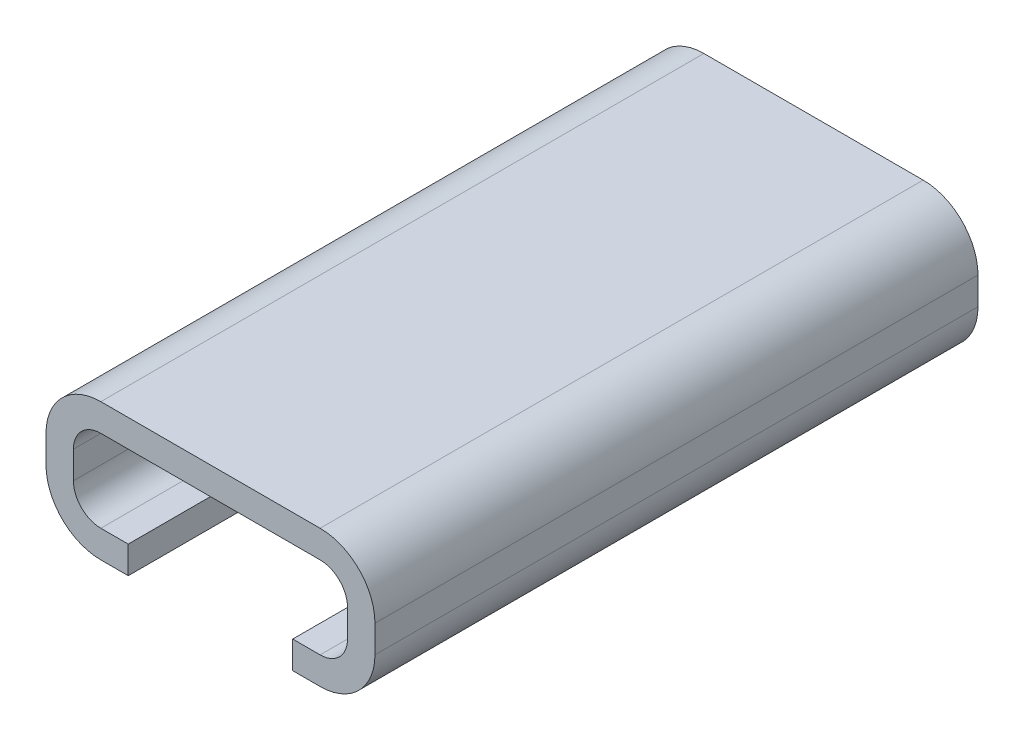
SolidWorks part; units mm, degrees
ref_plane "Plan de face" through (0, 0, 0) normal (0, 0, 1) x (1, 0, 0)
ref_plane "Plan de dessus" through (0, 0, 0) normal (0, 1, 0) x (1, 0, 0)
ref_plane "Plan de droite" through (0, 0, 0) normal (1, 0, 0) x (0, 0, -1)
sketch "Esquisse1" plane through (0, 0, 0) normal (0, 0, 1) x (1, 0, 0)
  line L1 (5, 0.5) -> (5, -0.5)
  line L2 (4, -1.5) -> (-4, -1.5)
  line L3 (-5, -0.5) -> (-5, 0.5)
  line L5 (6, 0.5) -> (6, -0.5)
  line L6 (4, -2.5) -> (-4, -2.5)
  line L7 (-6, -0.5) -> (-6, 0.5)
  line L16 (-4, 2.5) -> (4, 2.5) construction
  line L17 (4, 2.5) -> (-2.2321, 2.5)
  line L18 (-4, 2.5) -> (-2.2321, 2.5)
  line L19 (-4, 1.5) -> (4, 1.5)
  line L20 (-4, 1.5) -> (4, 1.5) construction
  arc A0 (-4, -1.5) -> (-5, -0.5) centre (-4, -0.5) cw
  arc A1 (5, -0.5) -> (4, -1.5) centre (4, -0.5) cw
  arc A2 (4, 1.5) -> (5, 0.5) centre (4, 0.5) cw
  arc A3 (-4, 1.5) -> (-5, 0.5) centre (-4, 0.5) ccw
  arc A4 (4, 2.5) -> (6, 0.5) centre (4, 0.5) cw
  arc A5 (6, -0.5) -> (4, -2.5) centre (4, -0.5) cw
  arc A6 (-4, -2.5) -> (-6, -0.5) centre (-4, -0.5) cw
  arc A7 (-4, 2.5) -> (-6, 0.5) centre (-4, 0.5) ccw
  point P6 (-5, -1.5)
  point P11 (5.1, 1.6)
  point P14 (-5, 1.5)
  point P15 (0, 1.5)
  point P16 (-5, 0)
  dimension "D3" = 1
  dimension "D1" = 3
  dimension "D2" = 10
  dimension "D9" = 3
  dimension "D4" = 1
extrude "Boss.-Extru.2" add sketch "Esquisse1" along normal blind 10
sketch "Esquisse7" plane through (0, 0, 0) normal (0, 0, -1) x (-1, 0, 0)
  line L8 (-6, 0.5) -> (-6, -0.5)
  line L9 (-4, -2.5) -> (4, -2.5)
  line L10 (6, -0.5) -> (6, 0.5)
  line L11 (4, 2.5) -> (-4, 2.5)
  line L16 (-6, 0.5) -> (-6, -0.5)
  line L17 (-4, -2.5) -> (4, -2.5)
  line L18 (6, -0.5) -> (6, 0.5)
  line L19 (4, 2.5) -> (-4, 2.5)
  arc A8 (-4, 2.5) -> (-6, 0.5) centre (-4, 0.5) ccw
  arc A9 (-6, -0.5) -> (-4, -2.5) centre (-4, -0.5) ccw
  arc A10 (4, -2.5) -> (6, -0.5) centre (4, -0.5) ccw
  arc A11 (6, 0.5) -> (4, 2.5) centre (4, 0.5) ccw
  arc A16 (-4, 2.5) -> (-6, 0.5) centre (-4, 0.5) ccw
  arc A17 (-6, -0.5) -> (-4, -2.5) centre (-4, -0.5) ccw
  arc A18 (4, -2.5) -> (6, -0.5) centre (4, -0.5) ccw
  arc A19 (6, 0.5) -> (4, 2.5) centre (4, 0.5) ccw
  dimension "D1" = 0
extrude "Boss.-Extru.4" add sketch "Esquisse7" along normal blind 1
mirror "Symétrie1" about plane through (4, 0.5, -1) normal (0, 0, -1) of "Boss.-Extru.4", "Boss.-Extru.2"
sketch "Esquisse5" plane through (0, -2.5, 0) normal (0, -1, 0) x (1, 0, 0)
  line L0 (4, -12) -> (-4, -12) construction
  line L1 (3, -12) -> (-3, -12)
  line L2 (3, -12) -> (3, -2)
  line L3 (3, -2) -> (-3, -2)
  line L4 (-3, -12) -> (-3, -2)
  line L5 (4, 10) -> (-4, 10) construction
  line L6 (-3, 10) -> (3, 10)
  line L7 (-3, 10) -> (-3, 0)
  line L8 (-3, 0) -> (3, 0)
  line L9 (3, 10) -> (3, 0)
  line L10 (-4, 10) -> (-4, -12) construction
  line L11 (4, 10) -> (4, -12) construction
  dimension "D1" = 10
  dimension "D2" = 10
  dimension "D3" = 1
  dimension "D4" = 1
extrude "Enlèv. mat.-Extru.1" cut sketch "Esquisse5" against normal up to surface (1 mm away) up to face at (0, -1.5, -7)
